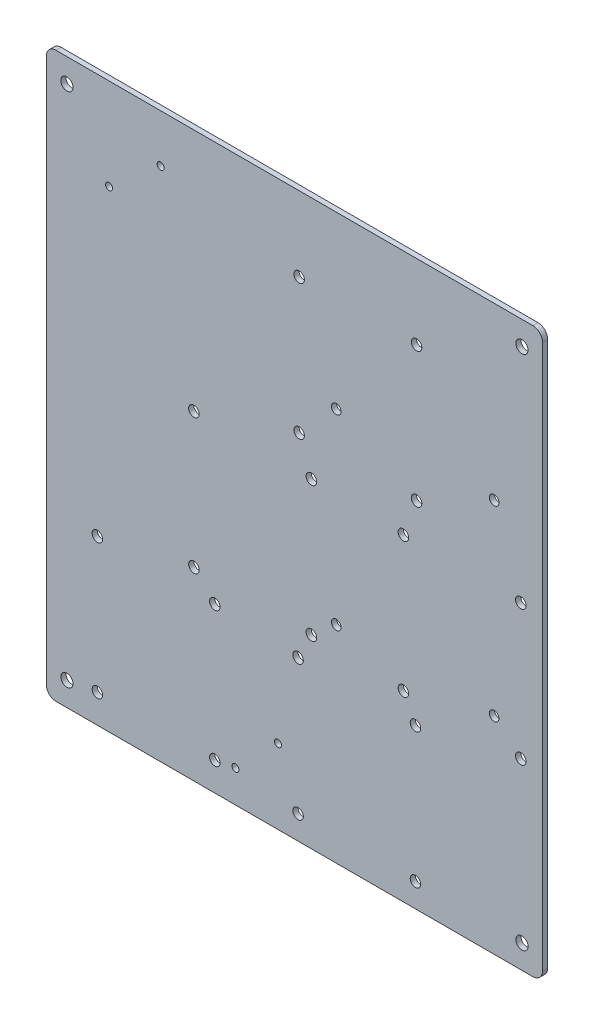
SolidWorks part; units mm, degrees
material "6061-T6 (SS)"
ref_plane "Front Plane" through (0, 0, 0) normal (0, 0, 1) x (1, 0, 0)
ref_plane "Top Plane" through (0, 0, 0) normal (0, 1, 0) x (1, 0, 0)
ref_plane "Right Plane" through (0, 0, 0) normal (1, 0, 0) x (0, 0, -1)
sketch "Sketch1" plane through (0, 0, 0) normal (0, 0, 1) x (1, 0, 0)
  line L1 (-77, -87.5) -> (77, -87.5)
  line L2 (-77, -87.5) -> (-77, 87.5)
  line L3 (-77, 87.5) -> (77, 87.5)
  line L4 (77, -87.5) -> (77, 87.5)
  line L5 (0, 87.5) -> (0, -87.5) construction
  line L6 (-77, 0) -> (77, 0) construction
  point P0 (0, 0)
  dimension "D1" = 175
  dimension "D2" = 154
extrude "Boss-Extrude1" add sketch "Sketch1" along normal blind 1.6
fillet "Fillet1" radius 3 4 edges at (77, -87.5, 0.8) (-77, -87.5, 0.8) (77, 87.5, 0.8) (-77, 87.5, 0.8)
sketch "Sketch2" plane through (0, 0, 1.6) normal (0, 0, 1) x (1, 0, 0)
  line L1 (-70.612, -80.137) -> (70.612, -80.137) construction
  line L2 (-70.612, -80.137) -> (-70.612, 80.137) construction
  line L3 (-70.612, 80.137) -> (70.612, 80.137) construction
  line L4 (70.612, -80.137) -> (70.612, 80.137) construction
  line L5 (0, 80.137) -> (0, -80.137) construction
  line L6 (-70.612, 0) -> (70.612, 0) construction
  circle A0 centre (-70.612, 80.137) radius 1.8987
  circle A1 centre (70.612, 80.137) radius 1.8987
  circle A2 centre (70.612, -80.137) radius 1.8987
  circle A3 centre (-70.612, -80.137) radius 1.8987
  point P0 (0, 0)
  dimension "D3" = 3.7973
  dimension "D1" = 141.224
  dimension "D2" = 160.274
extrude "Cut-Extrude1" cut sketch "Sketch2" against normal through all
sketch "Sketch3" plane through (0, 0, 1.6) normal (0, 0, 1) x (1, 0, 0)
  line L0 (33.8136, -30.7591) -> (70.2626, -30.7591) construction
  line L1 (1.4604, 22.4005) -> (37.9094, 22.4005) construction
  line L2 (1.4604, 22.4005) -> (1.4604, 64.3105) construction
  line L3 (1.4604, 64.3105) -> (37.9094, 64.3105) construction
  line L4 (37.9094, 22.4005) -> (37.9094, 64.3105) construction
  line L5 (19.6849, 64.3105) -> (19.6849, 22.4005) construction
  line L6 (1.4604, 43.3555) -> (37.9094, 43.3555) construction
  line L7 (33.8136, -30.7591) -> (33.8136, 11.1509) construction
  line L8 (33.8136, 11.1509) -> (70.2626, 11.1509) construction
  line L9 (70.2626, -30.7591) -> (70.2626, 11.1509) construction
  line L10 (52.0381, 11.1509) -> (52.0381, -30.7591) construction
  line L11 (33.8136, -9.8041) -> (70.2626, -9.8041) construction
  line L12 (1.1268, -80.0977) -> (37.5758, -80.0977) construction
  line L13 (1.1268, -80.0977) -> (1.1268, -38.1877) construction
  line L14 (1.1268, -38.1877) -> (37.5758, -38.1877) construction
  line L15 (37.5758, -80.0977) -> (37.5758, -38.1877) construction
  line L16 (19.3513, -38.1877) -> (19.3513, -80.0977) construction
  line L17 (1.1268, -59.1427) -> (37.5758, -59.1427) construction
  line L18 (-31.19, -30.019) -> (5.259, -30.019) construction
  line L19 (-31.19, -30.019) -> (-31.19, 11.891) construction
  line L20 (-31.19, 11.891) -> (5.259, 11.891) construction
  line L21 (5.259, -30.019) -> (5.259, 11.891) construction
  line L22 (-12.9655, 11.891) -> (-12.9655, -30.019) construction
  line L23 (-31.19, -9.064) -> (5.259, -9.064) construction
  line L24 (-61.1633, -78.6176) -> (-24.7143, -78.6176) construction
  line L25 (-61.1633, -78.6176) -> (-61.1633, -36.7076) construction
  line L26 (-61.1633, -36.7076) -> (-24.7143, -36.7076) construction
  line L27 (-24.7143, -78.6176) -> (-24.7143, -36.7076) construction
  line L28 (-42.9388, -36.7076) -> (-42.9388, -78.6176) construction
  line L29 (-61.1633, -57.6626) -> (-24.7143, -57.6626) construction
  circle A0 centre (1.4604, 64.3105) radius 1.6319
  circle A1 centre (37.9094, 64.3105) radius 1.6319
  circle A2 centre (37.9094, 22.4005) radius 1.6319
  circle A3 centre (1.4604, 22.4005) radius 1.632
  circle A4 centre (33.8136, 11.1509) radius 1.632
  circle A5 centre (70.2626, 11.1509) radius 1.632
  circle A6 centre (70.2626, -30.7591) radius 1.6319
  circle A7 centre (33.8136, -30.7591) radius 1.6319
  circle A8 centre (1.1268, -38.1877) radius 1.632
  circle A9 centre (37.5758, -38.1877) radius 1.632
  circle A10 centre (37.5758, -80.0977) radius 1.6319
  circle A11 centre (1.1268, -80.0977) radius 1.632
  circle A12 centre (-31.19, 11.891) radius 1.632
  circle A13 centre (5.259, 11.891) radius 1.632
  circle A14 centre (5.259, -30.019) radius 1.6319
  circle A15 centre (-31.19, -30.019) radius 1.6319
  circle A16 centre (-61.1633, -36.7076) radius 1.6319
  circle A17 centre (-24.7143, -36.7076) radius 1.632
  circle A18 centre (-24.7143, -78.6176) radius 1.6319
  circle A19 centre (-61.1633, -78.6176) radius 1.6319
  point P0 (19.6849, 43.3555)
  point P8 (-0.7456, 33.7043)
  point P9 (52.0381, -9.8041)
  point P22 (19.6849, 43.3555)
  point P23 (0, 0)
  point P24 (19.3513, -59.1427)
  point P37 (-12.9655, -9.064)
  point P50 (-42.9388, -57.6626)
  dimension "D3" = 3.2639
  dimension "D1" = 36.449
  dimension "D2" = 41.91
extrude "Cut-Extrude2" cut sketch "Sketch3" against normal through all
sketch "Sketch4" plane through (0, 0, 1.6) normal (0, 0, 1) x (1, 0, 0)
  line L1 (12.986, -23.4183) -> (61.986, -23.4183) construction
  line L2 (12.986, -23.4183) -> (12.986, 34.5817) construction
  line L3 (12.986, 34.5817) -> (61.986, 34.5817) construction
  line L4 (61.986, -23.4183) -> (61.986, 34.5817) construction
  line L5 (37.486, 34.5817) -> (37.486, -23.4183) construction
  line L6 (12.986, 5.5817) -> (61.986, 5.5817) construction
  circle A0 centre (12.986, 34.5817) radius 1.5
  circle A1 centre (61.986, 34.5817) radius 1.5
  circle A2 centre (61.986, -23.4183) radius 1.5
  circle A3 centre (12.986, -23.4183) radius 1.5
  point P0 (37.486, 5.5817)
  point P8 (37.486, 5.5817)
  dimension "D3" = 3
  dimension "D1" = 49
  dimension "D2" = 58
extrude "Cut-Extrude3" cut sketch "Sketch4" against normal through all
sketch "Sketch5" plane through (0, 0, 0) normal (0, 0, -1) x (-1, 0, 0)
  circle A0 centre (41.5189, 72.6317) radius 1.09
  circle A1 centre (57.5189, 59.1317) radius 1.09
  circle A2 centre (18.3018, -77.5283) radius 1.09
  circle A3 centre (5.1018, -64.3283) radius 1.09
  point P8 (-12.6303, -78.2078)
  point P9 (18.3018, -77.5283)
  dimension "D1" = 13.5
  dimension "D3" = 2.18
  dimension "D4" = 13.2
  dimension "D2" = 16
  dimension "D5" = 13.2
extrude "Cut-Extrude4" cut sketch "Sketch5" against normal through all
